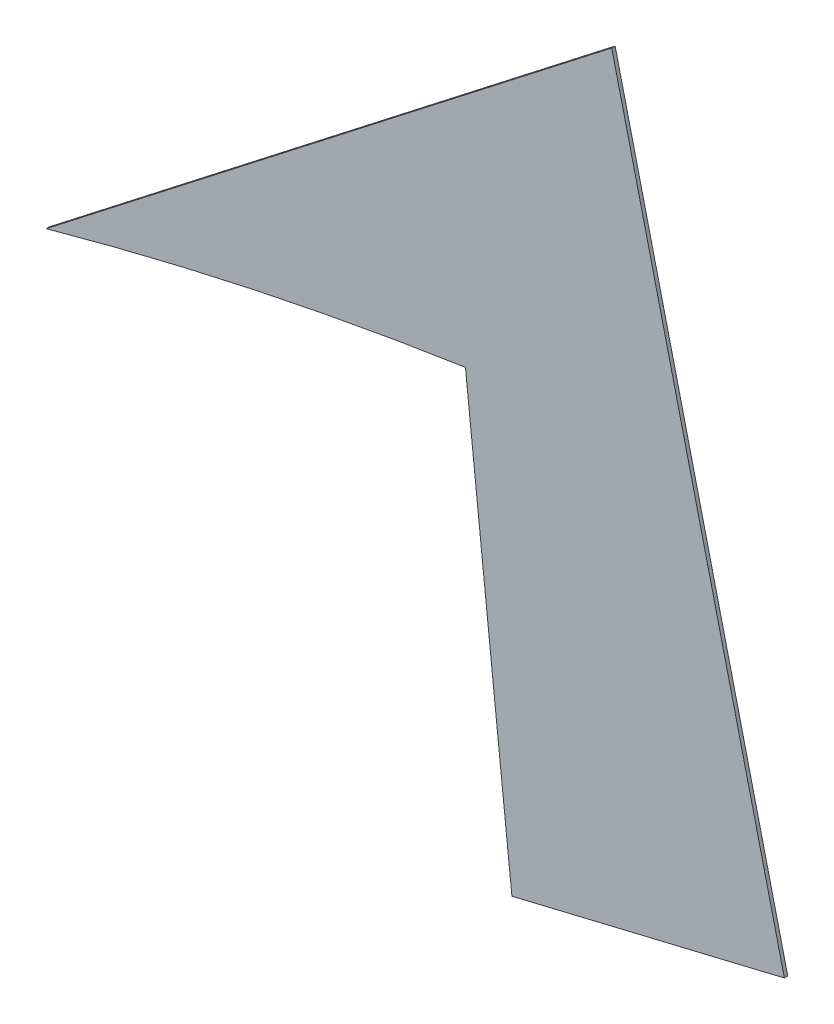
SolidWorks part; units mm, degrees
ref_plane "Alzado" through (0, 0, 0) normal (0, 0, 1) x (1, 0, 0)
ref_plane "Planta" through (0, 0, 0) normal (0, 1, 0) x (1, 0, 0)
ref_plane "Vista lateral" through (0, 0, 0) normal (1, 0, 0) x (0, 0, -1)
sketch "Model" plane through (0, 0, 0) normal (0, 0, 1) x (1, 0, 0)
  line L0 (24.5735, 10.3978) -> (16.5861, 8.4804)
  line L1 (16.5861, 8.4804) -> (15.2237, 21.2265)
  line L2 (2.9336, 18.6029) -> (19.5126, 31.4804)
  line L3 (19.5126, 31.4804) -> (24.5735, 10.3978)
  arc A0 (15.2237, 21.2265) -> (2.9336, 18.6029) centre (30.7069, -81.4039) ccw
extrude "Saliente-Extruir1" add sketch "Model" along normal blind 0.1
